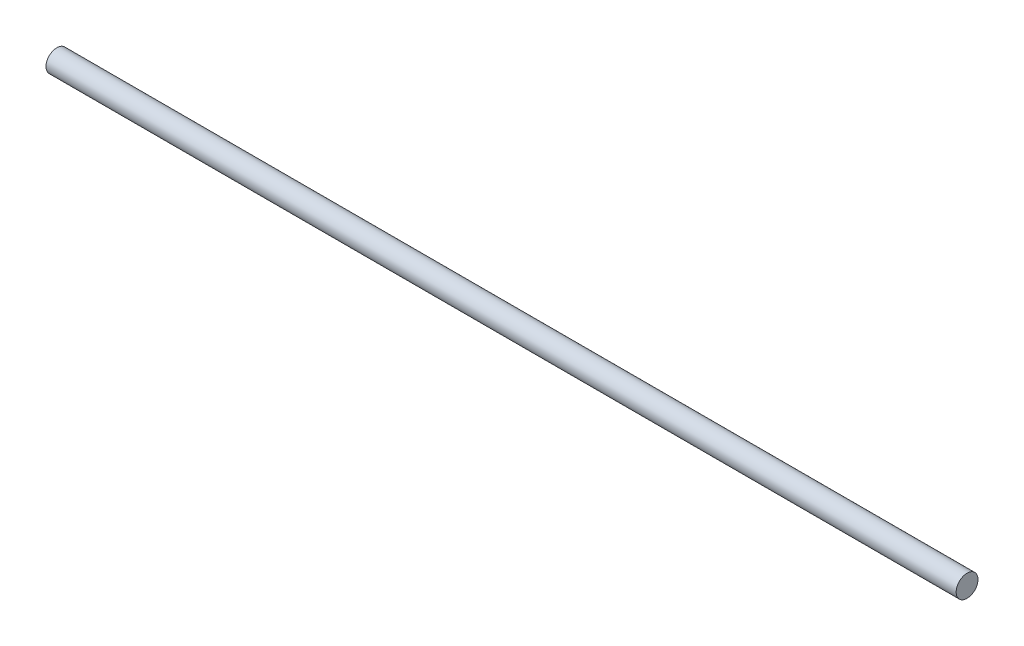
SolidWorks part; units mm, degrees
ref_plane "Plano frontal" through (0, 0, 0) normal (0, 0, 1) x (1, 0, 0)
ref_plane "Plano superior" through (0, 0, 0) normal (0, 1, 0) x (1, 0, 0)
ref_plane "Plano direito" through (0, 0, 0) normal (1, 0, 0) x (0, 0, -1)
sketch "Esboço1" plane through (0, 0, 0) normal (1, 0, 0) x (0, 0, -1)
  circle A0 centre (0, 0) radius 3
  dimension "D1" = 6
extrude "Ressalto-extrusão1" add sketch "Esboço1" along normal blind 250
